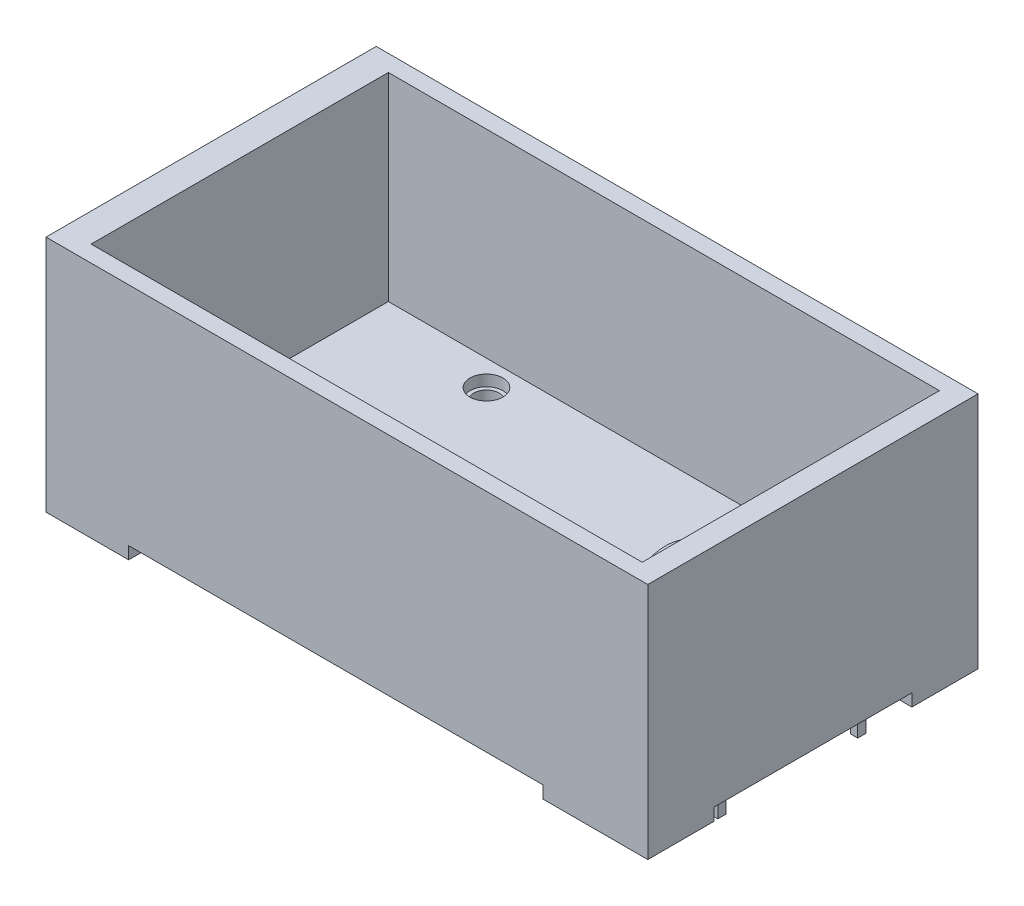
SolidWorks part; units mm, degrees
material "PUR"
ref_plane "Спереди" through (0, 0, 0) normal (0, 0, 1) x (1, 0, 0)
ref_plane "Сверху" through (0, 0, 0) normal (0, 1, 0) x (1, 0, 0)
ref_plane "Справа" through (0, 0, 0) normal (1, 0, 0) x (0, 0, -1)
sketch "Эскиз1" plane through (0, 0, 0) normal (0, 1, 0) x (1, 0, 0)
  line L1 (-27.305, 14.985) -> (27.305, 14.985)
  line L2 (-27.305, 14.985) -> (-27.305, -14.985)
  line L3 (-27.305, -14.985) -> (27.305, -14.985)
  line L4 (27.305, 14.985) -> (27.305, -14.985)
  line L5 (-27.305, 14.985) -> (27.305, -14.985) construction
  line L6 (-27.305, -14.985) -> (27.305, 14.985) construction
  point P0 (0, 0)
  dimension "D1" = 29.97
  dimension "D2" = 54.61
extrude "Бобышка-Вытянуть1" add sketch "Эскиз1" along normal blind 2.5
sketch "Эскиз2" plane through (0, 2.5, 0) normal (0, 1, 0) x (1, 0, 0)
  line L0 (27.305, -14.985) -> (-0.695, -14.985)
  line L1 (-27.305, -14.985) -> (27.305, -14.985) construction
  line L2 (-0.695, -14.985) -> (-0.695, -13.485)
  line L3 (-0.695, -13.485) -> (23.305, -13.485)
  line L4 (25.305, -11.485) -> (25.305, 11.485)
  line L5 (27.305, -14.985) -> (27.305, 14.985)
  line L6 (27.305, -14.985) -> (27.305, 14.985) construction
  line L7 (34.4496, 0) -> (-14.6404, 0) construction
  line L8 (27.305, 14.985) -> (-0.695, 14.985)
  line L9 (-0.695, 14.985) -> (-0.695, 13.485)
  line L10 (-0.695, 13.485) -> (23.305, 13.485)
  arc A0 (25.305, -11.485) -> (23.305, -13.485) centre (23.305, -11.485) cw
  arc A1 (25.305, 11.485) -> (23.305, 13.485) centre (23.305, 11.485) ccw
  point P17 (27.305, 0)
  point P22 (25.305, 0)
  dimension "D4" = 2
  dimension "D1" = 1.5
  dimension "D2" = 2
  dimension "D3" = 28
extrude "Бобышка-Вытянуть2" add sketch "Эскиз2" along normal blind 17
sketch "Эскиз3" plane through (0, 0, 14.985) normal (0, 0, 1) x (1, 0, 0)
  line L0 (-0.695, 2.5) -> (25.305, 19.5)
  line L1 (-0.695, 19.5) -> (27.305, 19.5) construction
  line L2 (25.305, 19.5) -> (-0.695, 19.5)
  line L3 (-0.695, 19.5) -> (-0.695, 2.5)
extrude "Вырез-Вытянуть1" cut sketch "Эскиз3" against normal through all
sketch "Эскиз4" plane through (0, 2.5, 0) normal (0, 1, 0) x (1, 0, 0)
  line L0 (0, 0) -> (36.3439, 0) construction
  line L1 (-34.9908, 11.175) -> (34.2331, 11.175) construction
  line L2 (-15.0193, -11.175) -> (34.2331, -11.175) construction
  line L3 (27.305, -14.985) -> (27.305, 14.985) construction
  circle A0 centre (-13.495, 11.175) radius 1.145
  circle A1 centre (-0.005, -11.175) radius 1.145
  circle A2 centre (13.475, 11.175) radius 1.145
  dimension "D1" = 2.29
  dimension "D2" = 22.35
  dimension "D3" = 27.31
  dimension "D4" = 13.49
  dimension "D5" = 26.97
extrude "Вырез-Вытянуть2" cut sketch "Эскиз4" against normal through all
sketch "Эскиз5" plane through (0, 0, 0) normal (0, -1, 0) x (1, 0, 0)
  line L1 (-27.305, 14.985) -> (-19.805, 14.985)
  line L2 (-27.305, 14.985) -> (-27.305, 8.985)
  line L3 (-27.305, 8.985) -> (-19.805, 8.985)
  line L4 (-19.805, 14.985) -> (-19.805, 8.985)
  line L5 (27.305, 14.985) -> (17.805, 14.985)
  line L6 (27.305, 14.985) -> (27.305, 8.985)
  line L7 (27.305, 8.985) -> (17.805, 8.985)
  line L8 (17.805, 14.985) -> (17.805, 8.985)
  line L9 (27.305, -14.985) -> (17.805, -14.985)
  line L10 (27.305, -14.985) -> (27.305, -8.985)
  line L11 (27.305, -8.985) -> (17.805, -8.985)
  line L12 (17.805, -14.985) -> (17.805, -8.985)
  line L13 (-27.305, -14.985) -> (-19.805, -14.985)
  line L14 (-27.305, -14.985) -> (-27.305, -8.985)
  line L15 (-27.305, -8.985) -> (-19.805, -8.985)
  line L16 (-19.805, -14.985) -> (-19.805, -8.985)
  circle A0 centre (-0.005, 11.175) radius 2.25
  circle A1 centre (13.475, -11.175) radius 2.25
  circle A2 centre (-13.495, -11.175) radius 2.25
  dimension "D1" = 4.5
  dimension "D2" = 6
  dimension "D3" = 9.5
  dimension "D4" = 7.5
extrude "Бобышка-Вытянуть3" add sketch "Эскиз5" along direction (0, -1, 0) on the side of the normal offset from surface (1.12 mm away) 20.62
sketch "Эскиз6" plane through (0, 2.5, 0) normal (0, 1, 0) x (1, 0, 0)
  circle A15 centre (-13.495, 11.175) radius 1.145
  circle A16 centre (-13.495, 11.175) radius 1.145
  circle A18 centre (13.475, 11.175) radius 1.145
  circle A19 centre (13.475, 11.175) radius 1.145
  circle A21 centre (-0.005, -11.175) radius 1.145
  circle A22 centre (-0.005, -11.175) radius 1.145
  dimension "D1" = 0
  dimension "D2" = 0
  dimension "D3" = 0
extrude "Вырез-Вытянуть3" cut sketch "Эскиз6" against normal through all
sketch "Эскиз7" plane through (0, 2.5, 0) normal (0, 1, 0) x (1, 0, 0)
  circle A0 centre (-13.495, 11.175) radius 1.5
  circle A1 centre (13.475, 11.175) radius 1.5
  circle A2 centre (-0.005, -11.175) radius 1.5
  dimension "D1" = 3
extrude "Вырез-Вытянуть4" cut sketch "Эскиз7" against normal blind 1
sketch "Эскиз9" plane through (0, 0, 0) normal (0, -1, 0) x (1, 0, 0)
  line L0 (25.075, 20.363) -> (25.075, -22.124) construction
  line L1 (36.5427, 0) -> (8.3422, 0) construction
  line L2 (24.745, 5.97) -> (25.405, 5.97)
  line L3 (24.745, -6.73) -> (25.405, -6.73)
  line L4 (24.745, -6.73) -> (24.745, -5.97)
  line L5 (24.745, -5.97) -> (25.405, -5.97)
  line L6 (25.405, -6.73) -> (25.405, -5.97)
  line L7 (24.745, -6.73) -> (25.405, -5.97) construction
  line L8 (24.745, -5.97) -> (25.405, -6.73) construction
  line L9 (25.405, 6.73) -> (25.405, 5.97)
  line L10 (24.745, 6.73) -> (25.405, 6.73)
  line L11 (24.745, 6.73) -> (24.745, 5.97)
  circle A0 centre (13.475, -11.175) radius 1.145 construction
  point P4 (25.075, -6.35)
  dimension "D4" = 11.6
  dimension "D1" = 0.76
  dimension "D2" = 0.66
  dimension "D3" = 12.7
extrude "Бобышка-Вытянуть5" add sketch "Эскиз9" along normal blind 3
sketch "Эскиз10" plane through (25.305, 0, 0) normal (-1, 0, 0) x (0, 0, 1)
  line L0 (-18.4903, 11.48) -> (20.51, 11.48) construction
  line L1 (0, 0) -> (0, 20.3244) construction
  line L2 (-14.985, -1.12) -> (-8.985, -1.12) construction
  circle A0 centre (-6.35, 11.48) radius 3.75
  circle A1 centre (6.35, 11.48) radius 3.75
  dimension "D3" = 7.5
  dimension "D1" = 12.6
  dimension "D2" = 12.7
extrude "Бобышка-Вытянуть6" add sketch "Эскиз10" along normal blind 1
sketch "Эскиз11" plane through (24.305, 0, 0) normal (-1, 0, 0) x (0, 0, 1)
  circle A0 centre (-6.35, 11.48) radius 3
  circle A1 centre (-6.35, 11.48) radius 2
  dimension "D1" = 6
  dimension "D2" = 4
extrude "Бобышка-Вытянуть7" add sketch "Эскиз11" along normal blind 4
sketch "Эскиз12" plane through (24.305, 0, 0) normal (-1, 0, 0) x (0, 0, 1)
  circle A0 centre (6.35, 11.48) radius 4.25
  circle A1 centre (6.35, 11.48) radius 3.25
  dimension "D1" = 8.5
  dimension "D2" = 6.5
extrude "Бобышка-Вытянуть8" add sketch "Эскиз12" along normal blind 4
sketch "Sketch5" plane through (0, 19.5, 0) normal (0, 1, 0) x (1, 0, 0)
  line L5 (25.305, -14.985) -> (-0.695, -14.985)
  line L6 (25.305, -14.985) -> (25.305, -10.985)
  line L7 (25.305, -10.985) -> (-0.695, -10.985)
  line L8 (-0.695, -14.985) -> (-0.695, -10.985)
  line L9 (25.305, 14.985) -> (-0.695, 14.985)
  line L10 (25.305, 14.985) -> (25.305, 10.985)
  line L11 (25.305, 10.985) -> (-0.695, 10.985)
  line L12 (-0.695, 14.985) -> (-0.695, 10.985)
  dimension "D1" = 26
  dimension "D2" = 4
  dimension "D3" = 4
  dimension "D4" = 26
extrude "Cut-Extrude4" cut sketch "Sketch5" against normal blind 17
sketch "Sketch6" plane through (0, 2.5, 0) normal (0, 1, 0) x (1, 0, 0)
  line L0 (25.305, 13.485) -> (25.305, 14.985)
  line L5 (-24.705, 13.485) -> (25.305, 13.485)
  line L6 (-24.705, 13.485) -> (-24.705, -13.485)
  line L7 (-24.705, -13.485) -> (25.305, -13.485)
  line L9 (25.305, 14.985) -> (-27.305, 14.985)
  line L10 (-27.305, 14.985) -> (-27.305, -14.985)
  line L11 (-27.305, -14.985) -> (25.305, -14.985)
  line L12 (25.305, -14.985) -> (25.305, -13.485)
extrude "Boss-Extrude1" add sketch "Sketch6" along normal blind 18
sketch "Sketch7" plane through (0, 19.5, 0) normal (0, 1, 0) x (1, 0, 0)
  line L1 (25.305, 14.985) -> (27.305, 14.985)
  line L2 (25.305, 14.985) -> (25.305, -14.985)
  line L3 (25.305, -14.985) -> (27.305, -14.985)
  line L4 (27.305, 14.985) -> (27.305, -14.985)
extrude "Boss-Extrude2" add sketch "Sketch7" along normal blind 1
